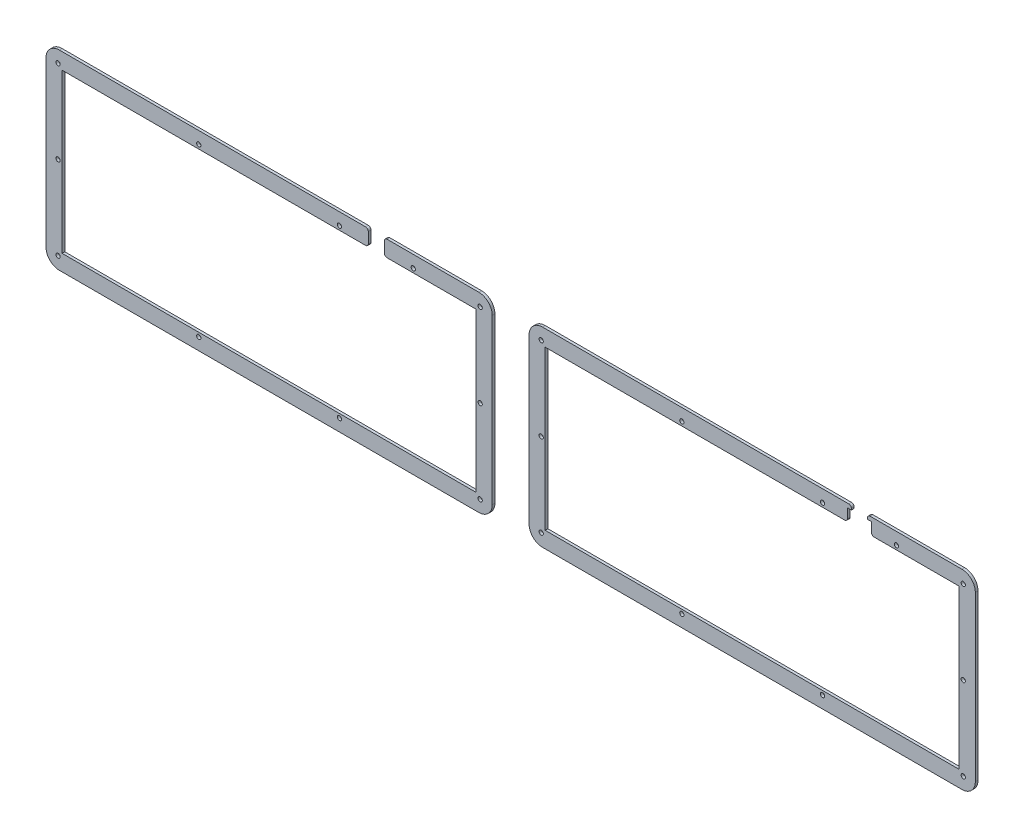
SolidWorks part; units mm, degrees
ref_plane "前视基准面" through (0, 0, 0) normal (0, 0, 1) x (1, 0, 0)
ref_plane "上视基准面" through (0, 0, 0) normal (0, 1, 0) x (1, 0, 0)
ref_plane "右视基准面" through (0, 0, 0) normal (1, 0, 0) x (0, 0, -1)
sketch "草图1" plane through (0, 0, 0) normal (0, 0, 1) x (1, 0, 0)
  line L0 (-119.2466, 73.6099) -> (-119.2466, 67.6099)
  line L1 (-121.2466, 64.6099) -> (-347.6476, 64.6099)
  line L2 (-347.6476, 64.6099) -> (-347.6476, -53.6908)
  line L3 (-347.6476, -53.6908) -> (-38.8456, -53.6908)
  line L4 (-38.8456, -53.6908) -> (-38.8456, 64.6099)
  line L5 (-38.8456, 64.6099) -> (-105.2466, 64.6099)
  line L6 (-107.2466, 67.6099) -> (-107.2466, 73.6099)
  line L7 (-26.8456, 66.6099) -> (-26.8456, -55.6922)
  line L8 (-36.8456, -65.6922) -> (-349.6475, -65.6922)
  line L9 (-359.6475, -55.6922) -> (-359.6475, 66.6099)
  line L10 (-36.8456, 76.6099) -> (-105.2466, 76.6099)
  line L11 (-353.6475, 70.6099) -> (-32.8456, 70.6099) construction
  line L12 (-353.6475, 70.6099) -> (-353.6475, -59.6922) construction
  line L13 (-353.6475, -59.6922) -> (-32.8456, -59.6922) construction
  line L14 (-32.8456, 70.6099) -> (-32.8456, -59.6922) construction
  line L15 (-121.2466, 76.6099) -> (-349.6475, 76.6099)
  line L16 (12.6771, 65.855) -> (12.6771, -52.4457)
  line L17 (12.6771, -52.4457) -> (321.4791, -52.4457)
  line L18 (321.4791, -52.4457) -> (321.4791, 65.855)
  line L19 (333.4791, 67.855) -> (333.4791, -54.4471)
  line L20 (323.4791, -64.4471) -> (10.6771, -64.4471)
  line L21 (0.6771, -54.4471) -> (0.6771, 67.855)
  line L22 (6.6771, 71.855) -> (327.4791, 71.855) construction
  line L23 (6.6771, 71.855) -> (6.6771, -58.4471) construction
  line L24 (6.6771, -58.4471) -> (327.4791, -58.4471) construction
  line L25 (327.4791, 71.855) -> (327.4791, -58.4471) construction
  line L26 (10.6771, 77.855) -> (236.0781, 77.855)
  line L27 (12.6771, 65.855) -> (236.0781, 65.855)
  line L28 (258.0781, 77.855) -> (323.4791, 77.855)
  line L29 (321.4791, 65.855) -> (258.0781, 65.855)
  line L30 (-119.2466, 66.6099) -> (-119.2466, 67.6099)
  line L31 (-119.2466, 73.6099) -> (-119.2466, 74.6099)
  line L32 (-107.2466, 74.6099) -> (-107.2466, 73.6099)
  line L33 (-107.2466, 67.6099) -> (-107.2466, 66.6099)
  line L34 (238.0781, 67.855) -> (238.0781, 74.855)
  line L35 (256.0781, 67.855) -> (256.0781, 74.855)
  line L36 (239.0781, 77.855) -> (236.0781, 77.855)
  line L37 (253.0781, 75.855) -> (253.0781, 74.855)
  line L38 (241.0781, 75.855) -> (241.0781, 74.855)
  line L39 (255.0781, 77.855) -> (258.0781, 77.855)
  line L40 (241.0781, 74.855) -> (238.0781, 74.855)
  line L41 (253.0781, 74.855) -> (256.0781, 74.855)
  circle A0 centre (-140.7806, 67.6099) radius 1.6
  circle A1 centre (-85.7126, 67.6099) radius 1.6
  circle A2 centre (-245.7136, 67.6099) radius 1.6
  circle A3 centre (-350.6475, 67.6099) radius 1.6
  circle A4 centre (-350.6475, 5.4588) radius 1.5998
  circle A5 centre (-350.6475, -56.6922) radius 1.5999
  circle A6 centre (-245.7136, -56.6922) radius 1.5999
  circle A7 centre (-140.7806, -56.6922) radius 1.5999
  circle A8 centre (-35.8456, -56.6922) radius 1.5999
  circle A9 centre (-35.8456, 5.4588) radius 1.5998
  circle A10 centre (-35.8456, 67.6099) radius 1.6
  arc A11 (-349.6475, 76.6099) -> (-359.6475, 66.6099) centre (-349.6475, 66.6099) ccw
  arc A12 (-359.6475, -55.6922) -> (-349.6475, -65.6922) centre (-349.6475, -55.6922) ccw
  arc A13 (-36.8456, -65.6922) -> (-26.8456, -55.6922) centre (-36.8456, -55.6922) ccw
  arc A14 (-26.8456, 66.6099) -> (-36.8456, 76.6099) centre (-36.8456, 66.6099) ccw
  circle A15 centre (219.5441, 68.855) radius 1.6
  circle A16 centre (274.6121, 68.855) radius 1.6
  circle A17 centre (114.6111, 68.855) radius 1.6
  circle A18 centre (9.6771, 68.855) radius 1.6
  circle A19 centre (9.6771, 6.7039) radius 1.5998
  circle A20 centre (9.6771, -55.4471) radius 1.5999
  circle A21 centre (114.6111, -55.4471) radius 1.5999
  circle A22 centre (219.5441, -55.4471) radius 1.5999
  circle A23 centre (324.4791, -55.4471) radius 1.5999
  circle A24 centre (324.4791, 6.7039) radius 1.5998
  circle A25 centre (324.4791, 68.855) radius 1.6
  arc A26 (10.6771, 77.855) -> (0.6771, 67.855) centre (10.6771, 67.855) ccw
  arc A27 (0.6771, -54.4471) -> (10.6771, -64.4471) centre (10.6771, -54.4471) ccw
  arc A28 (323.4791, -64.4471) -> (333.4791, -54.4471) centre (323.4791, -54.4471) ccw
  arc A29 (333.4791, 67.855) -> (323.4791, 77.855) centre (323.4791, 67.855) ccw
  arc A30 (256.0781, 67.855) -> (258.0781, 65.855) centre (258.0781, 67.855) ccw
  arc A31 (238.0781, 67.855) -> (236.0781, 65.855) centre (236.0781, 67.855) cw
  arc A32 (-107.2466, 74.6099) -> (-105.2466, 76.6099) centre (-105.2466, 74.6099) cw
  arc A33 (-107.2466, 66.6099) -> (-105.2466, 64.6099) centre (-105.2466, 66.6099) ccw
  arc A34 (-121.2466, 64.6099) -> (-119.2466, 66.6099) centre (-121.2466, 66.6099) ccw
  arc A35 (-119.2466, 74.6099) -> (-121.2466, 76.6099) centre (-121.2466, 74.6099) ccw
  arc A36 (253.0781, 75.855) -> (255.0781, 77.855) centre (255.0781, 75.855) cw
  arc A37 (241.0781, 75.855) -> (239.0781, 77.855) centre (239.0781, 75.855) ccw
  dimension "D1" = 3.2
  dimension "D3" = 10
  dimension "D4" = 3.2
  dimension "D6" = 10
  dimension "D7" = 2
  dimension "D8" = 2
  dimension "D2" = 55.068
  dimension "D5" = 55.068
extrude "凸台-拉伸1" add sketch "草图1" along normal blind 2
